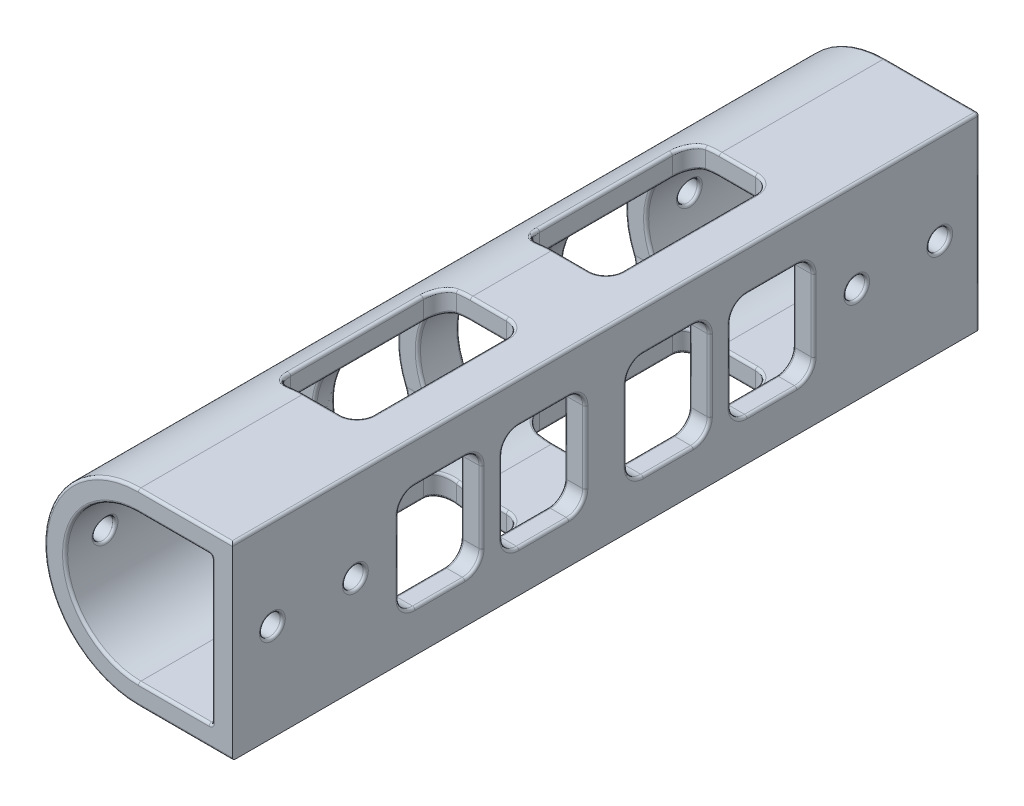
SolidWorks part; units mm, degrees
ref_plane "Front Plane" through (0, 0, 0) normal (0, 0, 1) x (1, 0, 0)
ref_plane "Top Plane" through (0, 0, 0) normal (0, 1, 0) x (1, 0, 0)
ref_plane "Right Plane" through (0, 0, 0) normal (1, 0, 0) x (0, 0, -1)
sketch "Sketch1" plane through (0, 0, 0) normal (0, 0, 1) x (1, 0, 0)
  line L1 (0, 13.9792) -> (14.3954, 13.9792)
  line L2 (0, 13.9792) -> (0, -14.8117)
  line L3 (0, -14.8117) -> (14.3955, -14.8117)
  line L4 (14.3954, 13.9792) -> (14.3955, -14.8117)
  line L5 (11.2204, -11.6367) -> (0, -11.6367)
  line L6 (11.2204, -11.6367) -> (11.2204, 10.8042)
  line L7 (11.2204, 10.8042) -> (0, 10.8042)
  line L8 (0, -11.6367) -> (0, 10.8042)
  arc A0 (0, -11.6367) -> (0, 10.8042) centre (0, -0.4163) cw
  arc A1 (0, 13.9792) -> (0, -14.8117) centre (0, -0.4163) ccw
  dimension "D1" = 28.7909
  dimension "D2" = 14.3954
  dimension "D3" = 3.175
  dimension "D4" = 3.175
  dimension "D5" = 3.175
extrude "Boss-Extrude1" add sketch "Sketch1" along normal blind 114.3 contours L2 A1 A0 | L7 L6 L5 L2 L3 L4 L1
sketch "Sketch3" plane through (0, 0, 0) normal (1, 0, 0) x (0, 0, -1)
  line L6 (0, 13.9792) -> (0, -14.8117) construction
  line L11 (-114.3, -11.6367) -> (0, -11.6367) construction
  line L12 (-86.36, -8.4617) -> (-78.74, -8.4617)
  line L13 (-88.9, -5.9217) -> (-88.9, 5.0892)
  line L14 (-86.36, 7.6292) -> (-78.74, 7.6292)
  line L15 (-76.2, -5.9217) -> (-76.2, 5.0892)
  line L17 (-114.3, 10.8042) -> (0, 10.8042) construction
  line L18 (-114.3, -11.6367) -> (-114.3, 10.8042) construction
  line L22 (-70.485, -8.4617) -> (-62.865, -8.4617)
  line L23 (-73.025, -5.9217) -> (-73.025, 5.0892)
  line L24 (-70.485, 7.6292) -> (-62.865, 7.6292)
  line L25 (-60.325, -5.9217) -> (-60.325, 5.0892)
  line L26 (-35.56, -8.4617) -> (-27.94, -8.4617)
  line L27 (-38.1, -5.9217) -> (-38.1, 5.0892)
  line L28 (-35.56, 7.6292) -> (-27.94, 7.6292)
  line L29 (-25.4, -5.9217) -> (-25.4, 5.0892)
  line L31 (-51.435, -8.4617) -> (-43.815, -8.4617)
  line L32 (-53.975, -5.9217) -> (-53.975, 5.0892)
  line L33 (-51.435, 7.6292) -> (-43.815, 7.6292)
  line L34 (-41.275, -5.9217) -> (-41.275, 5.0892)
  arc A3 (-76.2, 5.0892) -> (-78.74, 7.6292) centre (-78.74, 5.0892) ccw
  arc A4 (-78.74, -8.4617) -> (-76.2, -5.9217) centre (-78.74, -5.9217) ccw
  arc A5 (-88.9, -5.9217) -> (-86.36, -8.4617) centre (-86.36, -5.9217) ccw
  arc A6 (-88.9, 5.0892) -> (-86.36, 7.6292) centre (-86.36, 5.0892) cw
  arc A7 (-38.1, 5.0892) -> (-35.56, 7.6292) centre (-35.56, 5.0892) cw
  arc A8 (-25.4, 5.0892) -> (-27.94, 7.6292) centre (-27.94, 5.0892) ccw
  arc A9 (-27.94, -8.4617) -> (-25.4, -5.9217) centre (-27.94, -5.9217) ccw
  arc A10 (-60.325, -5.9217) -> (-62.865, -8.4617) centre (-62.865, -5.9217) cw
  arc A11 (-60.325, 5.0892) -> (-62.865, 7.6292) centre (-62.865, 5.0892) ccw
  arc A12 (-73.025, 5.0892) -> (-70.485, 7.6292) centre (-70.485, 5.0892) cw
  arc A13 (-73.025, -5.9217) -> (-70.485, -8.4617) centre (-70.485, -5.9217) ccw
  arc A14 (-38.1, -5.9217) -> (-35.56, -8.4617) centre (-35.56, -5.9217) ccw
  arc A15 (-41.275, 5.0892) -> (-43.815, 7.6292) centre (-43.815, 5.0892) ccw
  arc A16 (-53.975, 5.0892) -> (-51.435, 7.6292) centre (-51.435, 5.0892) cw
  arc A17 (-51.435, -8.4617) -> (-53.975, -5.9217) centre (-51.435, -5.9217) cw
  arc A18 (-43.815, -8.4617) -> (-41.275, -5.9217) centre (-43.815, -5.9217) ccw
  point P28 (-76.2, -0.4163)
  point P49 (-47.625, 7.6292)
  dimension "D2" = 3.175
  dimension "D4" = 12.7
  dimension "D5" = 2.54
  dimension "D14" = 2.54
  dimension "D15" = 2.54
  dimension "D20" = 2.54
  dimension "D1" = 3.175
  dimension "D3" = 25.4
  dimension "D6" = 25.4
  dimension "D7" = 12.7
  dimension "D8" = 3.175
  dimension "D9" = 12.7
  dimension "D10" = 3.175
  dimension "D11" = 3.175
  dimension "D12" = 3.175
  dimension "D13" = 3.175
  dimension "D16" = 12.7
  dimension "D17" = 6.35
  dimension "D18" = 3.175
  dimension "D19" = 3.175
extrude "Cut-Extrude1" cut sketch "Sketch3" against normal blind 25.4 and the other way blind 25.4
sketch "Sketch6" plane through (0, 0, 0) normal (0, 1, 0) x (1, 0, 0)
  line L5 (0, -114.3) -> (14.3954, -114.3) construction
  line L6 (-2.1145, -25.4) -> (5.5054, -25.4)
  line L11 (-4.6546, -27.94) -> (-4.6545, -48.26)
  line L12 (-2.1145, -50.8) -> (5.5054, -50.8)
  line L13 (8.0454, -27.94) -> (8.0455, -48.26)
  line L14 (5.5054, -88.9) -> (-2.1145, -88.9)
  line L15 (8.0454, -86.36) -> (8.0454, -66.04)
  line L16 (5.5054, -63.5) -> (-2.1145, -63.5)
  line L17 (-4.6546, -86.36) -> (-4.6546, -66.04)
  line L18 (11.2204, -114.3) -> (11.2204, 0) construction
  line L19 (0, 0) -> (14.3954, 0) construction
  arc A0 (-2.1145, -88.9) -> (-4.6546, -86.36) centre (-2.1146, -86.36) cw
  arc A1 (8.0454, -86.36) -> (5.5054, -88.9) centre (5.5054, -86.36) cw
  arc A2 (-2.1145, -63.5) -> (-4.6546, -66.04) centre (-2.1146, -66.04) ccw
  arc A3 (8.0454, -66.04) -> (5.5054, -63.5) centre (5.5054, -66.04) ccw
  arc A4 (-2.1145, -50.8) -> (-4.6545, -48.26) centre (-2.1145, -48.26) cw
  arc A5 (5.5054, -50.8) -> (8.0455, -48.26) centre (5.5055, -48.26) ccw
  arc A6 (-2.1145, -25.4) -> (-4.6546, -27.94) centre (-2.1146, -27.94) ccw
  arc A7 (5.5054, -25.4) -> (8.0454, -27.94) centre (5.5054, -27.94) cw
  point P21 (8.0454, -88.9)
  point P26 (8.0454, -63.5)
  dimension "D7" = 2.54
  dimension "D1" = 25.4
  dimension "D2" = 25.4
  dimension "D3" = 3.175
  dimension "D4" = 12.7
  dimension "D5" = 25.4
  dimension "D6" = 25.4
extrude "Cut-Extrude2" cut sketch "Sketch6" against normal blind 25.4 and the other way blind 25.4
sketch "Sketch7" plane through (0, 0, 0) normal (1, 0, 0) x (0, 0, -1)
  line L0 (-114.3, 0) -> (0, 0) construction
  line L2 (-114.3, 13.9792) -> (-114.3, -14.8117) construction
  line L3 (-57.15, -21.0207) -> (-57.15, 21.0207)
  line L6 (0, 13.9792) -> (0, -14.8117) construction
  circle A0 centre (-108.204, 0) radius 1.5875
  circle A1 centre (-95.504, 0) radius 1.5875
  circle A2 centre (-18.796, 0) radius 1.5875
  circle A3 centre (-6.096, 0) radius 1.5875
  point P3 (-111.5194, 0)
  point P12 (-57.15, 0)
  point P13 (-57.15, 0)
  dimension "D2" = 3.175
  dimension "D1" = 6.096
  dimension "D3" = 12.7
  dimension "D4" = 6.096
extrude "Cut-Extrude3" cut sketch "Sketch7" against normal blind 25.4 and the other way blind 25.4 contours A3 | A2 | A1 | A0
fillet "Fillet3" radius 0.3969 242 edges at (2.7527, -14.8117, 25.4) (-1.0602, -14.7726, 25.4) (-3.7235, 13.4893, 25.9746) (-3.9296, -14.265, 26.1632) (-4.6546, 13.2059, 38.1) (-4.6546, -14.0384, 38.1) (2.7527, -14.8117, 63.5) (-1.0602, -14.7726, 63.5) (-3.7235, 13.4893, 64.0746) (-3.9296, -14.265, 64.2632) (-4.6546, 13.2059, 76.2) (-4.6546, -14.0384, 76.2) (-7.8211, 7.6292, 31.75) (-8.9167, 6.3948, 25.7612) (-11.2204, -0.4163, 25.4) (-7.8211, 7.6292, 66.675) (-8.9167, 6.3948, 60.6862) (-11.2204, -0.4163, 60.325) (-7.8211, 7.6292, 47.625) (-8.9167, 6.3948, 41.6362) (-11.2204, -0.4163, 41.275) (-7.8211, 7.6292, 82.55) (-8.9167, 6.3948, 76.5612) (-11.2204, -0.4163, 76.2) (5.6102, 10.8042, 114.3) (7.1977, -14.8117, 114.3) (14.3954, -0.4163, 25.4) (14.3954, 6.8852, 26.1439) (14.3954, 7.6292, 31.75) (14.3954, -0.4163, 60.325) (14.3954, 6.8852, 61.0689) (14.3954, 7.6292, 66.675) (14.3954, -0.4163, 41.275) (14.3954, 6.8852, 42.0189) (14.3954, 7.6292, 47.625) (14.3954, -0.4163, 76.2) (14.3954, 6.8852, 76.9439) (14.3954, 7.6292, 82.55) (2.7527, 10.8042, 25.4) (-1.062, 10.7538, 25.4) (-3.7003, -11.009, 25.9558) (-3.9799, 10.0746, 26.216) (-4.6546, -10.6257, 38.1) (-4.6546, 9.7932, 38.1) (2.7527, 10.8042, 63.5) (-1.062, 10.7538, 63.5) (-3.7003, -11.009, 64.0558) (-3.9799, 10.0746, 64.316) (-4.6546, -10.6257, 76.2) (-4.6546, 9.7932, 76.2) (14.3954, 1.5875, 108.204) (11.2204, 0, 109.7915) (-11.1946, 0.3452, 106.6545) (-14.3953, -0.3557, 106.6569) (14.3954, 1.5875, 95.504) (11.2204, 0, 97.0915) (-11.1946, 0.3452, 93.9545) (-14.3953, -0.3557, 93.9569) (14.3954, 1.5875, 18.796) (11.2204, 0, 20.3835) (-11.2203, -0.3496, 17.2475) (-14.3749, 0.353, 17.2482) (14.3954, 1.5875, 6.096) (11.2204, 0, 7.6835) (-11.2203, -0.3496, 4.5475) (-14.3749, 0.353, 4.5482) (-1.062, -11.5863, 25.4) (2.7527, 13.9792, 25.4) (-1.0602, 13.9401, 25.4) (7.3015, 10.8042, 26.1439) (7.3015, -14.8117, 26.1439) (7.3015, 13.9792, 26.1439) (8.0455, 10.8042, 38.1) (8.0455, -14.8117, 38.1) (8.0455, 13.9792, 38.1) (7.3015, 10.8042, 50.0561) (7.3015, -14.8117, 50.0561) (7.3015, 13.9792, 50.0561) (-1.062, -11.5863, 50.8) (2.7527, 10.8042, 50.8) (-1.062, 10.7538, 50.8) (2.7527, -14.8117, 50.8) (-1.0602, -14.7726, 50.8) (2.7527, 13.9792, 50.8) (-1.0602, 13.9401, 50.8) (-1.062, -11.5863, 63.5) (2.7527, 13.9792, 63.5) (-1.0602, 13.9401, 63.5) (7.3015, 10.8042, 64.2439) (7.3015, -14.8117, 64.2439) (7.3015, 13.9792, 64.2439) (8.0454, 10.8042, 76.2) (8.0454, -14.8117, 76.2) (8.0454, 13.9792, 76.2) (7.3015, 10.8042, 88.1561) (7.3015, -14.8117, 88.1561) (7.3015, 13.9792, 88.1561) (-1.062, -11.5863, 88.9) (2.7527, 10.8042, 88.9) (-1.062, 10.7538, 88.9) (2.7527, -14.8117, 88.9) (-1.0602, -14.7726, 88.9) (2.7527, 13.9792, 88.9) (-1.0602, 13.9401, 88.9) (-3.9296, 13.4325, 50.0368) (-3.7235, -14.3218, 50.2254) (-3.9296, 13.4325, 88.1368) (-3.7235, -14.3218, 88.3254) (11.2204, 7.6292, 31.75) (-11.9373, 7.6292, 31.75) (11.2204, 6.8852, 26.1439) (-12.3169, 7.0351, 26.3075) (11.2204, -0.4163, 25.4) (-14.3954, -0.4163, 25.4) (11.2204, -7.7178, 26.1439) (-8.1547, -8.1234, 26.6734) (-12.4616, -7.6231, 26.054) (11.2204, -8.4617, 31.75) (-7.8211, -8.4617, 31.75) (-11.9373, -8.4617, 31.75) (11.2204, -7.7178, 37.3561) (-8.4657, -7.7804, 37.2911) (-12.1897, -8.0739, 36.9089) (11.2204, -0.4163, 38.1) (-11.2204, -0.4163, 38.1) (-14.3954, -0.4163, 38.1) (11.2204, 6.8852, 37.3561) (-10.584, 3.309, 33.7482) (-13.9576, 3.107, 33.9717) (11.2204, -8.4617, 66.675) (-7.8211, -8.4617, 66.675) (-11.9373, -8.4617, 66.675) (11.2204, -7.7178, 72.2811) (-8.4657, -7.7804, 72.2161) (-13.9064, -4.1365, 68.6782) (11.2204, -0.4163, 73.025) (-11.2204, -0.4163, 73.025) (-14.3954, -0.4163, 73.025) (11.2204, 6.8852, 72.2811) (-10.584, 3.309, 68.6732) (-12.4616, 6.7906, 72.371) (11.2204, 7.6292, 66.675) (-11.9373, 7.6292, 66.675) (11.2204, 6.8852, 61.0689) (-12.3169, 7.0351, 61.2325) (11.2204, -0.4163, 60.325) (-14.3954, -0.4163, 60.325) (11.2204, -7.7178, 61.0689) (-8.2858, -7.9822, 61.3797) (-12.6651, -7.259, 60.7055) (11.2204, -0.4163, 41.275) (-14.3954, -0.4163, 41.275) (11.2204, -7.7178, 42.0189) (-8.1547, -8.1234, 42.5484) (-12.4616, -7.6231, 41.929) (11.2204, -8.4617, 47.625) (-7.8211, -8.4617, 47.625) (-11.9373, -8.4617, 47.625) (11.2204, -7.7178, 53.2311) (-8.4657, -7.7804, 53.1661) (-13.9064, -4.1365, 49.6282) (11.2204, -0.4163, 53.975) (-11.2204, -0.4163, 53.975) (-14.3954, -0.4163, 53.975) (11.2204, 6.8852, 53.2311) (-10.584, 3.309, 49.6232) (-13.9576, 3.107, 49.8467) (11.2204, 7.6292, 47.625) (-11.9373, 7.6292, 47.625) (11.2204, 6.8852, 42.0189) (-12.3169, 7.0351, 42.1825) (11.2204, -0.4163, 76.2) (-14.3954, -0.4163, 76.2) (11.2204, -7.7178, 76.9439) (-8.2858, -7.9822, 77.2547) (-12.6651, -7.259, 76.5805) (11.2204, -8.4617, 82.55) (-7.8211, -8.4617, 82.55) (-11.9373, -8.4617, 82.55) (11.2204, -7.7178, 88.1561) (-10.6875, -3.8333, 84.9143) (-13.9064, -4.1365, 84.5532) (11.2204, -0.4163, 88.9) (-11.2204, -0.4163, 88.9) (-14.3954, -0.4163, 88.9) (11.2204, 6.8852, 88.1561) (-8.4, 7.0228, 88.0071) (-12.4616, 6.7906, 88.246) (11.2204, 7.6292, 82.55) (-11.9373, 7.6292, 82.55) (11.2204, 6.8852, 76.9439) (-12.3169, 7.0351, 77.1075) (-11.2204, -0.4163, 0) (5.6102, 10.8042, 0) (11.2204, -0.4163, 0) (5.6102, -11.6367, 0) (7.1977, 13.9792, 0) (-14.3954, -0.4163, 0) (7.1977, -14.8117, 0) (14.3954, -0.4163, 0) (-11.2204, -0.4163, 114.3) (11.2204, -0.4163, 114.3) (5.6102, -11.6367, 114.3) (7.1977, 13.9792, 114.3) (-14.3954, -0.4163, 114.3) (11.2204, -11.6367, 57.15) (11.2204, 10.8042, 57.15) (14.3954, 13.9792, 57.15) (14.3954, -7.7178, 26.1439) (14.3955, -8.4617, 31.75) (14.3955, -7.7178, 37.3561) (14.3954, -0.4163, 38.1) (14.3954, 6.8852, 37.3561) (14.3955, -8.4617, 66.675) (14.3955, -7.7178, 72.2811) (14.3954, -0.4163, 73.025) (14.3954, 6.8852, 72.2811) (14.3954, -7.7178, 61.0689) (14.3954, -7.7178, 42.0189) (14.3955, -8.4617, 47.625) (14.3955, -7.7178, 53.2311) (14.3954, -0.4163, 53.975) (14.3954, 6.8852, 53.2311) (14.3954, -7.7178, 76.9439) (14.3955, -8.4617, 82.55) (14.3955, -7.7178, 88.1561) (14.3954, -0.4163, 88.9) (14.3954, 6.8852, 88.1561) (2.7527, -11.6367, 25.4) (7.3015, -11.6367, 26.1439) (8.0455, -11.6367, 38.1) (7.3015, -11.6367, 50.0561) (2.7527, -11.6367, 50.8) (2.7527, -11.6367, 63.5) (7.3015, -11.6367, 64.2439) (8.0454, -11.6367, 76.2) (7.3015, -11.6367, 88.1561) (2.7527, -11.6367, 88.9) (-3.9799, -10.9072, 49.984) (-3.7003, 10.1765, 50.2442) (-3.9799, -10.9072, 88.084) (-3.7003, 10.1765, 88.3442)
